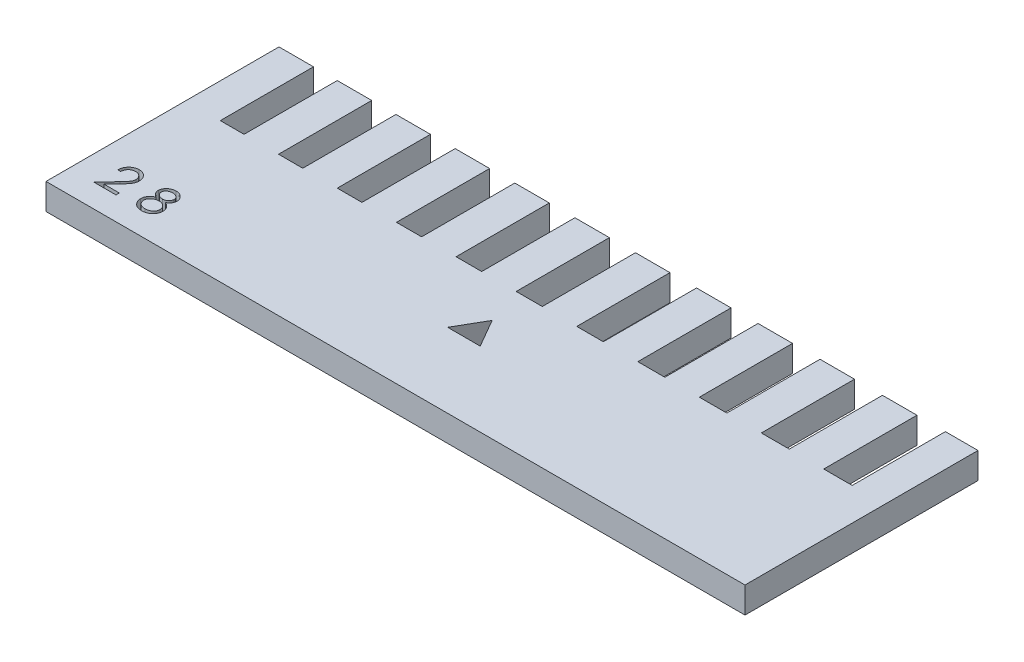
SolidWorks part; units mm, degrees
ref_plane "Ebene vorne" through (0, 0, 0) normal (0, 0, 1) x (1, 0, 0)
ref_plane "Ebene oben" through (0, 0, 0) normal (0, 1, 0) x (1, 0, 0)
ref_plane "Ebene rechts" through (0, 0, 0) normal (1, 0, 0) x (0, 0, -1)
sketch "Sketch1" plane through (0, 0, 0) normal (0, 1, 0) x (1, 0, 0)
  line L1 (0, 0) -> (75, 0)
  line L2 (0, 0) -> (0, 25)
  line L3 (0, 25) -> (75, 25)
  line L4 (75, 0) -> (75, 25)
  dimension "D1" = 75
  dimension "D2" = 25
extrude "Boss-Extrude1" add sketch "Sketch1" along normal blind 2.8
sketch "Sketch2" plane through (0, 2.8, 0) normal (0, 1, 0) x (1, 0, 0)
  line L0 (75, 25) -> (0, 25) construction
  line L1 (3.7, 25) -> (6.25, 25)
  line L2 (3.7, 25) -> (3.7, 15)
  line L3 (3.7, 15) -> (6.25, 15)
  line L4 (6.25, 25) -> (6.25, 15)
  line L5 (0, 25) -> (0, 0) construction
  line L6 (9.95, 25) -> (12.55, 25)
  line L7 (9.95, 25) -> (9.95, 15)
  line L8 (9.95, 15) -> (12.55, 15)
  line L9 (12.55, 25) -> (12.55, 15)
  line L10 (16.25, 25) -> (18.9, 25)
  line L11 (16.25, 25) -> (16.25, 15)
  line L12 (16.25, 15) -> (18.9, 15)
  line L13 (18.9, 25) -> (18.9, 15)
  line L14 (22.6, 25) -> (25.3, 25)
  line L15 (22.6, 25) -> (22.6, 15)
  line L16 (22.6, 15) -> (25.3, 15)
  line L17 (25.3, 25) -> (25.3, 15)
  line L18 (29, 25) -> (31.75, 25)
  line L19 (29, 25) -> (29, 15)
  line L20 (29, 15) -> (31.75, 15)
  line L21 (31.75, 25) -> (31.75, 15)
  line L22 (35.45, 25) -> (38.25, 25)
  line L23 (35.45, 25) -> (35.45, 15)
  line L24 (35.45, 15) -> (38.25, 15)
  line L25 (38.25, 25) -> (38.25, 15)
  line L26 (41.95, 25) -> (44.8, 25)
  line L27 (41.95, 25) -> (41.95, 15)
  line L28 (41.95, 15) -> (44.8, 15)
  line L29 (44.8, 25) -> (44.8, 15)
  line L30 (48.5, 25) -> (51.4, 25)
  line L31 (48.5, 25) -> (48.5, 15)
  line L32 (48.5, 15) -> (51.4, 15)
  line L33 (51.4, 25) -> (51.4, 15)
  line L34 (55.1, 25) -> (58.05, 25)
  line L35 (55.1, 25) -> (55.1, 15)
  line L36 (55.1, 15) -> (58.05, 15)
  line L37 (58.05, 25) -> (58.05, 15)
  line L38 (61.75, 25) -> (64.75, 25)
  line L39 (61.75, 25) -> (61.75, 15)
  line L40 (61.75, 15) -> (64.75, 15)
  line L41 (64.75, 25) -> (64.75, 15)
  line L42 (68.45, 25) -> (71.5, 25)
  line L43 (68.45, 25) -> (68.45, 15)
  line L44 (68.45, 15) -> (71.5, 15)
  line L45 (71.5, 25) -> (71.5, 15)
  line L46 (75, 0) -> (75, 25) construction
extrude "Cut-Extrude1" cut sketch "Sketch2" against normal through all
sketch "Sketch3" plane through (0, 2.8, 0) normal (0, 1, 0) x (1, 0, 0)
  line L0 (35.45, 25) -> (35.45, 15) construction
  line L1 (36.85, 11.0207) -> (35.1, 7.9896)
  line L2 (35.1, 7.9896) -> (38.6, 7.9896)
  line L3 (38.6, 7.9896) -> (36.85, 11.0207)
  line L6 (41.95, 25) -> (38.25, 25) construction
  circle A0 centre (36.85, 9) radius 1.0104 construction
extrude "Cut-Extrude2" cut sketch "Sketch3" against normal blind 2.8
sketch "Sketch5" plane through (0, 2.8, 0) normal (0, 1, 0) x (1, 0, 0)
  line L1 (0, 0) -> (75, 0) construction
  line L2 (0, 25) -> (0, 0) construction
  text T0 "2 8"
  dimension "D1" = 2.5
  dimension "D2" = 2.5
extrude "Cut-Extrude4" cut sketch "Sketch5" against normal blind 2.8
equation "\"D1@Sketch2\"=(\"Slot Width\")-0.05mm"
equation "\"D2@Sketch2\"=(\"Slot Width\")-0.1mm"
equation "\"D3@Sketch2\"=(\"Slot Width\")-0.15mm"
equation "\"D4@Sketch2\"=(\"Slot Width\")-0.2mm"
equation "\"D5@Sketch2\"=(\"Slot Width\")-0.25mm"
equation "\"D6@Sketch2\"=(\"Slot Width\")+0.05mm"
equation "\"D7@Sketch2\"=(\"Slot Width\")+0.1mm"
equation "\"D8@Sketch2\"=(\"Slot Width\")+0.15mm"
equation "\"D9@Sketch2\"=(\"Slot Width\")+0.2mm"
equation "\"D10@Sketch2\"=(\"Slot Width\")+0.25mm"
equation "\"D2@Sketch3\"=(\"Slot Width\")/2"
equation "\"D3@Sketch3\"=(\"Slot Depth\")+6mm"
